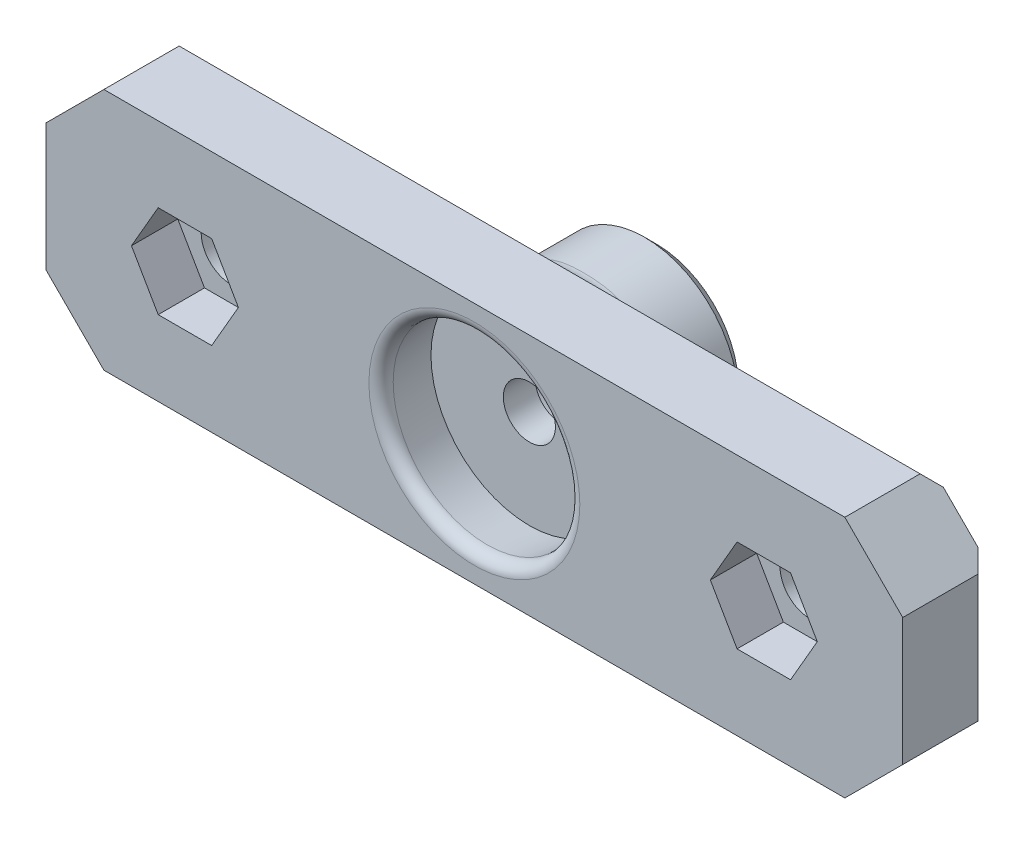
SolidWorks part; units mm, degrees
ref_plane "Front Plane" through (0, 0, 0) normal (0, 0, 1) x (1, 0, 0)
ref_plane "Top Plane" through (0, 0, 0) normal (0, 1, 0) x (1, 0, 0)
ref_plane "Right Plane" through (0, 0, 0) normal (1, 0, 0) x (0, 0, -1)
sketch "Sketch1" plane through (0, 0, 0) normal (0, 0, 1) x (1, 0, 0)
  line L1 (-37, -10.5) -> (37, -10.5)
  line L2 (-37, -10.5) -> (-37, 10.5)
  line L3 (-37, 10.5) -> (37, 10.5)
  line L4 (37, -10.5) -> (37, 10.5)
  line L5 (-37, -10.5) -> (37, 10.5) construction
  line L6 (-37, 10.5) -> (37, -10.5) construction
  point P0 (0, 0)
  dimension "D1" = 74
  dimension "D2" = 21
extrude "Boss-Extrude1" add sketch "Sketch1" along normal blind 7.5
sketch "Sketch2" plane through (0, 0, 7.5) normal (0, 0, 1) x (1, 0, 0)
  line L0 (-36.805, 0) -> (36.9536, 0) construction
  circle A0 centre (0, 0) radius 8
  dimension "D1" = 16
extrude "Cut-Extrude1" cut sketch "Sketch2" against normal blind 4.75 draft 6 draft outward yes
sketch "Sketch4" plane through (0, 0, 0) normal (0, 0, -1) x (-1, 0, 0)
  line L0 (-37, 0) -> (-25, 0) construction
  line L1 (-37, -10.5) -> (-37, 10.5) construction
  line L2 (0, 10.5) -> (0, -11.0022) construction
  line L3 (-37, 10.5) -> (37, 10.5) construction
  line L4 (37, 0) -> (25, 0) construction
  circle A0 centre (-25, 0) radius 2.6
  circle A1 centre (25, 0) radius 2.6
  dimension "D2" = 5.2
  dimension "D3" = 5.2
  dimension "D1" = 25
extrude "Cut-Extrude4" cut sketch "Sketch4" against normal through all
chamfer "Chamfer3" distance 5 angle 45 4 edges at (-37, 10.5, 3.75) (-37, -10.5, 3.75) (37, 10.5, 3.75) (37, -10.5, 3.75)
sketch "Sketch5" plane through (0, 0, 7.5) normal (0, 0, 1) x (1, 0, 0)
  line L0 (37, 0) -> (25, 0) construction
  line L1 (37, -5.5) -> (37, 5.5) construction
  line L2 (-37, 0) -> (-25, 0) construction
  line L3 (-37, 5.5) -> (-37, -5.5) construction
  line L5 (22.6906, -4) -> (27.3094, -4)
  line L6 (27.3094, -4) -> (29.6188, 0)
  line L7 (29.6188, 0) -> (27.3094, 4)
  line L8 (27.3094, 4) -> (22.6906, 4)
  line L9 (22.6906, 4) -> (20.3812, 0)
  line L10 (20.3812, 0) -> (22.6906, -4)
  line L11 (-27.3094, -4) -> (-22.6906, -4)
  line L12 (-22.6906, -4) -> (-20.3812, 0)
  line L13 (-20.3812, 0) -> (-22.6906, 4)
  line L14 (-22.6906, 4) -> (-27.3094, 4)
  line L15 (-27.3094, 4) -> (-29.6188, 0)
  line L16 (-29.6188, 0) -> (-27.3094, -4)
  circle A0 centre (25, 0) radius 4 construction
  circle A1 centre (-25, 0) radius 4 construction
  dimension "D1" = 8
  dimension "D2" = 8
extrude "Cut-Extrude6" cut sketch "Sketch5" against normal blind 4
sketch "Sketch11" plane through (0, 0, 7.5) normal (0, 0, 1) x (1, 0, 0)
  circle A0 centre (0, 0) radius 2.25
  dimension "D1" = 4.5
extrude "Cut-Extrude10" cut sketch "Sketch11" against normal through all
fillet "Fillet4" radius 1 2 edges at (-27.6, 0, 0) (22.4, 0, 0)
fillet "Fillet5" radius 1 1 edges at (8, 0, 7.5)
chamfer "Chamfer5" distance 1 angle 45 4 edges at (-37, 0, 0) (37, 0, 0) (0, 10.5, 0) (0, -10.5, 0)
sketch "Sketch12" plane through (0, 0, 0) normal (0, 0, -1) x (-1, 0, 0)
  circle A0 centre (0, 0) radius 6.1
  dimension "D1" = 12.2
extrude "Extrude-Thin1" add sketch "Sketch12" along normal blind 8.2 thin
fillet "Fillet6" radius 2 1 edges at (-8.1, 0, 0)
chamfer "Chamfer6" distance 1 angle 45 1 edges at (-8.1, 0, -8.2)
